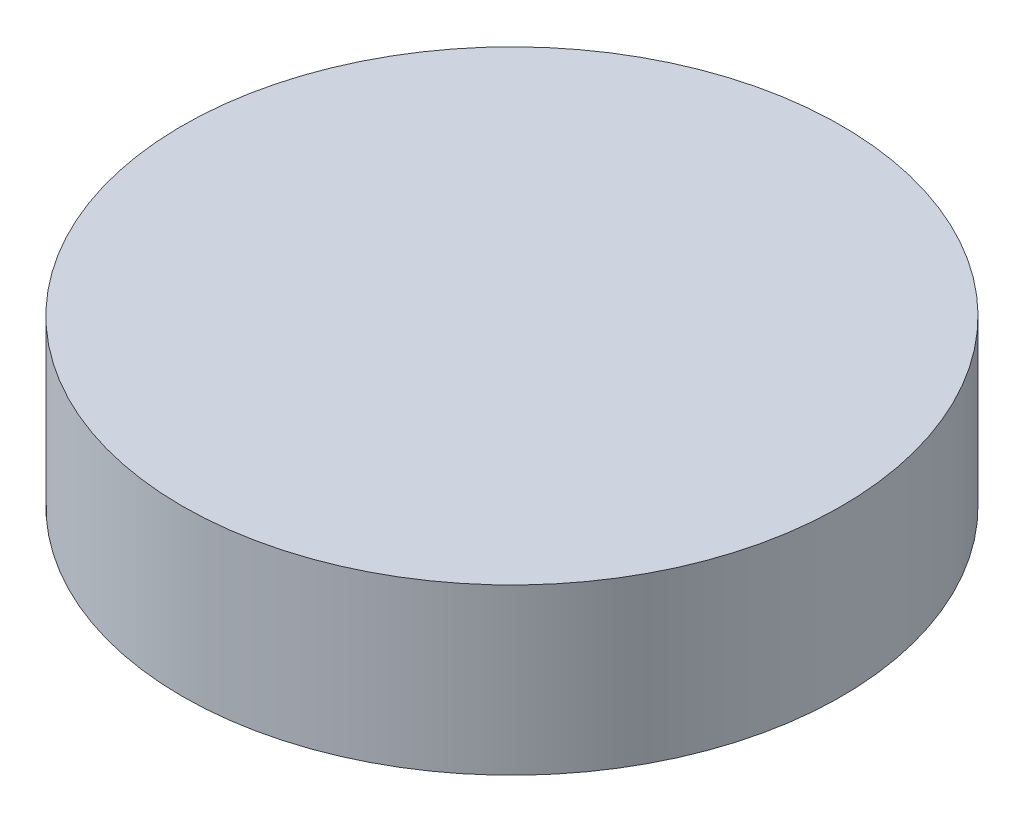
SolidWorks part; units mm, degrees
ref_plane "Спереди" through (0, 0, 0) normal (0, 0, 1) x (1, 0, 0)
ref_plane "Сверху" through (0, 0, 0) normal (0, 1, 0) x (1, 0, 0)
ref_plane "Справа" through (0, 0, 0) normal (1, 0, 0) x (0, 0, -1)
sketch "Эскиз1" plane through (0, 0, 0) normal (0, 1, 0) x (1, 0, 0)
  circle A0 centre (0, 0) radius 20
  dimension "D1" = 40
extrude "Бобышка-Вытянуть1" add sketch "Эскиз1" along normal blind 10
